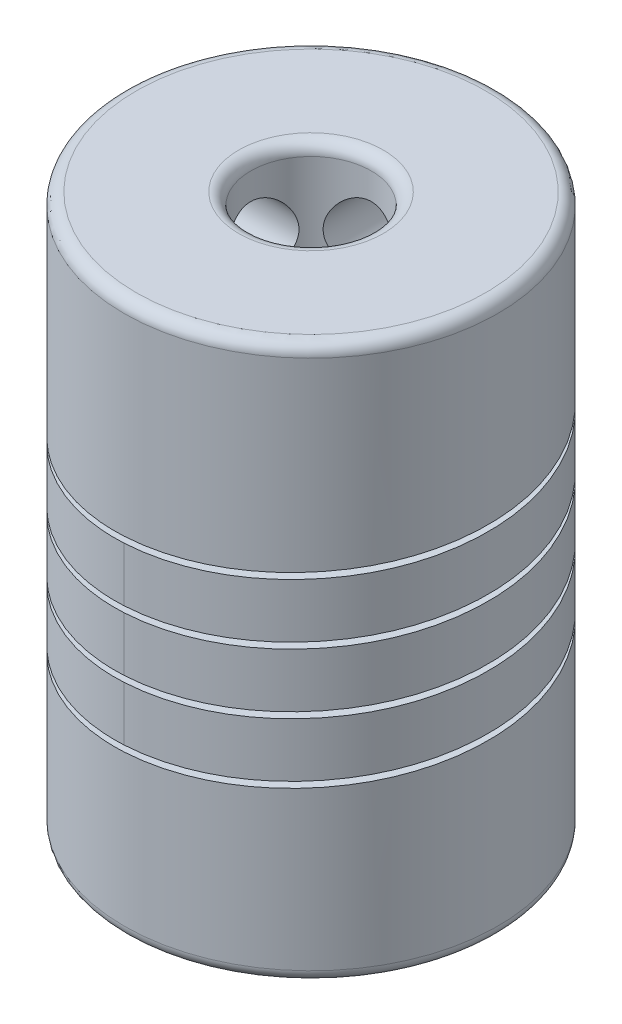
SolidWorks part; units mm, degrees
material "6063-T1"
ref_plane "Front Plane" through (0, 0, 0) normal (0, 0, 1) x (1, 0, 0)
ref_plane "Top Plane" through (0, 0, 0) normal (0, 1, 0) x (1, 0, 0)
ref_plane "Right Plane" through (0, 0, 0) normal (1, 0, 0) x (0, 0, -1)
sketch "Sketch1" plane through (0, 0, 0) normal (0, 1, 0) x (1, 0, 0)
  circle A0 centre (0, 0) radius 7.75
  dimension "D1" = 15.5
extrude "Boss-Extrude1" add sketch "Sketch1" along normal mid plane 23
sketch "Sketch2" plane through (0, 11.5, 0) normal (0, 1, 0) x (1, 0, 0)
  circle A0 centre (0, 0) radius 2.5
  dimension "D1" = 5
extrude "Cut-Extrude1" cut sketch "Sketch2" against normal blind 6
sketch "Sketch12" plane through (0, -11.5, 0) normal (0, -1, 0) x (1, 0, 0)
  circle A0 centre (0, 0) radius 4
  dimension "D1" = 8
extrude "Cut-Extrude3" cut sketch "Sketch12" against normal up to surface (17 mm away) up to face at (0, 5.5, 2.5)
ref_plane "Plane1" through (-7.75, 0, 0) normal (-1, 0, 0) x (0, 0, 1)
sketch "Sketch3" plane through (-7.75, 0, 0) normal (-1, 0, 0) x (0, 0, 1)
  line L0 (-40.9988, 0) -> (47.9686, 0) construction
  circle A0 centre (0, 8.4) radius 1.5
  circle A1 centre (0, -8.4) radius 1.5
  dimension "D1" = 8.4
  dimension "D2" = 3
extrude "Cut-Extrude2" cut sketch "Sketch3" against normal up to surface (5.75 mm away)
fillet "Fillet1" radius 0.5 2 edges at (0, 11.5, 7.75) (0, -11.5, 7.75)
fillet "Fillet3" radius 0.25 2 edges at (-7.6099, -8.0861, -1.4668) (-7.6099, 8.7139, -1.4668)
ref_plane "Plane2" through (0, -5, 0) normal (0, -1, 0) x (-1, 0, 0)
sketch "Sketch7" plane through (0, -5, 0) normal (0, -1, 0) x (-1, 0, 0)
  circle A0 centre (0, 0) radius 9.5211
curve "Helix/Spiral2" pitch 2.5 height 10 turns 4
sketch "Sketch8" plane through (0, 0, 0) normal (0, 0, 1) x (1, 0, 0)
  line L0 (-7.75, 6.65) -> (-7.75, -6.65) construction
  line L1 (-13.5, -2.6216) -> (-2, -2.6216)
  line L2 (-13.5, -2.6216) -> (-13.5, -2.8716)
  line L3 (-13.5, -2.8716) -> (-2, -2.8716)
  line L4 (-2, -2.6216) -> (-2, -2.8716)
  line L5 (-13.5, -2.6216) -> (-2, -2.8716) construction
  line L6 (-13.5, -2.8716) -> (-2, -2.6216) construction
  spline S0 degree 3 poles (-9.5211, -5) (-9.5211, -4.9483) (-9.0254, -4.8436) (-6.9077, -4.6875) (-3.7384, -4.5312) (0, -4.375) (3.7384, -4.2187) (6.9077, -4.0625) (9.0254, -3.9062) (9.769, -3.75) (9.0254, -3.5937) (6.9077, -3.4375) (3.7384, -3.2812) (0, -3.125) (-3.7384, -2.9687) (-6.9077, -2.8125) (-9.0254, -2.6562) (-9.769, -2.5) (-9.0254, -2.3437) (-6.9077, -2.1875) (-3.7384, -2.0312) (0, -1.875) (3.7384, -1.7187) (6.9077, -1.5625) (9.0254, -1.4062) (9.769, -1.25) (9.0254, -1.0937) (6.9077, -0.9375) (3.7384, -0.7812) (0, -0.625) (-3.7384, -0.4687) (-6.9077, -0.3125) (-9.0254, -0.1562) (-9.769, 0) (-9.0254, 0.1563) (-6.9077, 0.3125) (-3.7384, 0.4688) (0, 0.625) (3.7384, 0.7813) (6.9077, 0.9375) (9.0254, 1.0938) (9.769, 1.25) (9.0254, 1.4063) (6.9077, 1.5625) (3.7384, 1.7188) (0, 1.875) (-3.7384, 2.0312) (-6.9077, 2.1875) (-9.0254, 2.3437) (-9.769, 2.5) (-9.0254, 2.6562) (-6.9077, 2.8125) (-3.7384, 2.9687) (0, 3.125) (3.7384, 3.2812) (6.9077, 3.4375) (9.0254, 3.5937) (9.769, 3.75) (9.0254, 3.9062) (6.9077, 4.0625) (3.7384, 4.2187) (0, 4.375) (-3.7384, 4.5312) (-6.9077, 4.6875) (-9.0254, 4.8436) (-9.5211, 4.9483) (-9.5211, 5) knots 0 0 0 0 0.015625 0.03125 0.046875 0.0625 0.078125 0.09375 0.109375 0.125 0.140625 0.15625 0.171875 0.1875 0.203125 0.21875 0.234375 0.25 0.265625 0.28125 0.296875 0.3125 0.328125 0.34375 0.359375 0.375 0.390625 0.40625 0.421875 0.4375 0.453125 0.46875 0.484375 0.5 0.515625 0.53125 0.546875 0.5625 0.578125 0.59375 0.609375 0.625 0.640625 0.65625 0.671875 0.6875 0.703125 0.71875 0.734375 0.75 0.765625 0.78125 0.796875 0.8125 0.828125 0.84375 0.859375 0.875 0.890625 0.90625 0.921875 0.9375 0.953125 0.96875 0.984375 1 1 1 1 construction
  point P0 (-7.75, -2.7466)
  dimension "D1" = 0.25
  dimension "D2" = 2
sweep "Cut-Sweep2" cut profiles "Sketch8" path "Helix/Spiral2"
pattern_circular "CirPattern1" count 2 over 90 about axis through (0, 11, 0) along (0, 1, 0) of "Cut-Extrude2", "Fillet3"
fillet "Fillet4" radius 0.5 2 edges at (0, -11.5, -4) (0, 11.5, 2.5)
